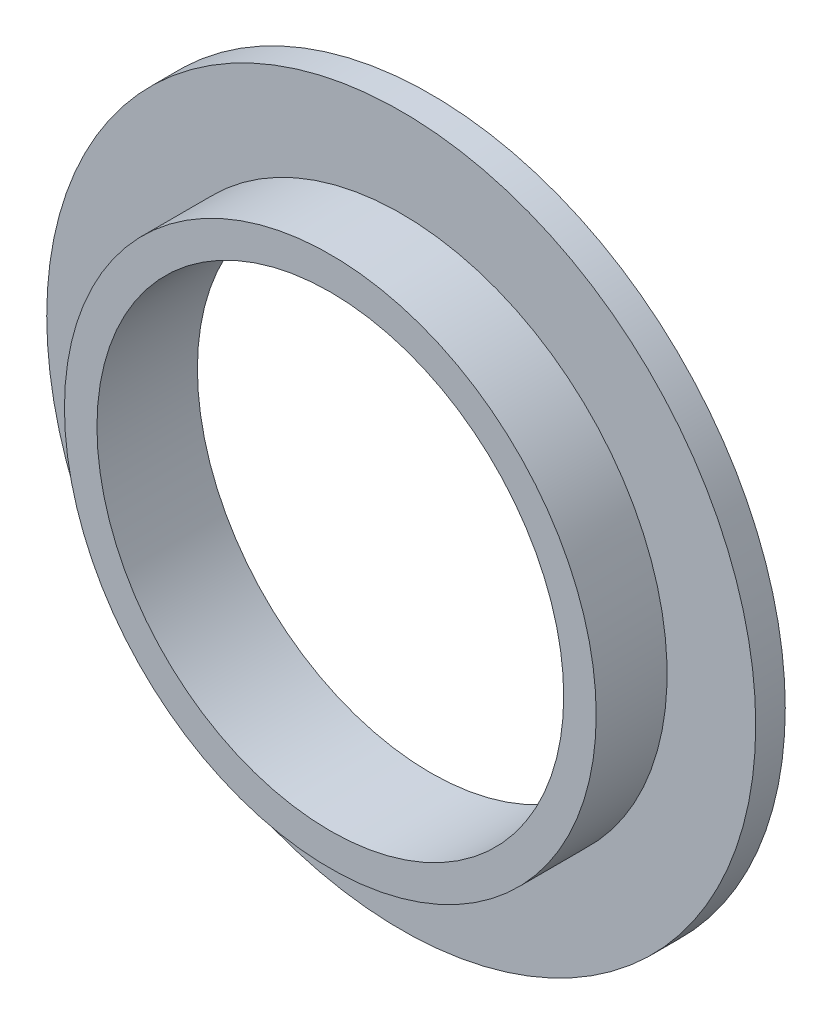
SolidWorks part; units mm, degrees
ref_plane "Front Plane" through (0, 0, 0) normal (0, 0, 1) x (1, 0, 0)
ref_plane "Top Plane" through (0, 0, 0) normal (0, 1, 0) x (1, 0, 0)
ref_plane "Right Plane" through (0, 0, 0) normal (1, 0, 0) x (0, 0, -1)
sketch "Sketch1" plane through (0, 0, 0) normal (0, 0, 1) x (1, 0, 0)
  circle A0 centre (0, 0) radius 25.0825
  circle A1 centre (0, 0) radius 28.575
  dimension "D1" = 50.165
  dimension "D2" = 57.15
extrude "Boss-Extrude1" add sketch "Sketch1" along normal blind 10.795
sketch "Sketch2" plane through (0, 0, 0) normal (0, 0, -1) x (-1, 0, 0)
  circle A0 centre (0, 0) radius 28.575
  circle A1 centre (0, 0) radius 38.1
  dimension "D1" = 76.2
extrude "Boss-Extrude2" add sketch "Sketch2" against normal blind 3.175
